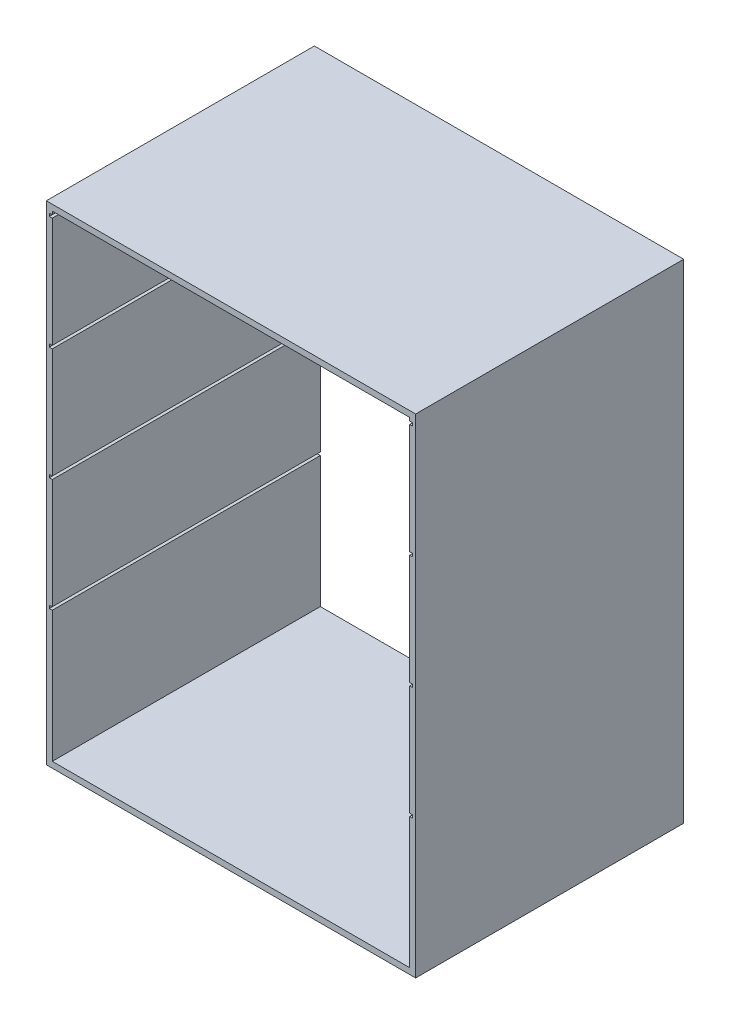
SolidWorks part; units mm, degrees
ref_plane "Front Plane" through (0, 0, 0) normal (0, 0, 1) x (1, 0, 0)
ref_plane "Top Plane" through (0, 0, 0) normal (0, 1, 0) x (1, 0, 0)
ref_plane "Right Plane" through (0, 0, 0) normal (1, 0, 0) x (0, 0, -1)
sketch "Sketch1" plane through (0, 0, 0) normal (0, 0, 1) x (1, 0, 0)
  line L1 (0, 0) -> (600, 0)
  line L2 (0, 0) -> (0, 800)
  line L3 (0, 800) -> (600, 800)
  line L4 (600, 0) -> (600, 800)
extrude "Extrude-Thin1" add sketch "Sketch1" along normal blind 450 thin
sketch "Sketch2" plane through (0, 0, 0) normal (0, 0, 1) x (1, 0, 0)
  line L0 (-5, 604.7007) -> (605, 604.7007)
  line L1 (-5, 604.7007) -> (-5, 599.7007)
  line L2 (-5, 599.7007) -> (605, 599.7007)
  line L3 (-5, 794.7007) -> (605, 794.7007)
  line L4 (605, 604.7007) -> (605, 599.7007)
  line L5 (-5, 414.7007) -> (605, 414.7007)
  line L6 (-5, 414.7007) -> (-5, 409.7007)
  line L7 (-5, 409.7007) -> (605, 409.7007)
  line L8 (605, 414.7007) -> (605, 409.7007)
  line L9 (-5, 224.7007) -> (605, 224.7007)
  line L10 (-5, 224.7007) -> (-5, 219.7007)
  line L11 (-5, 219.7007) -> (605, 219.7007)
  line L12 (605, 224.7007) -> (605, 219.7007)
  line L18 (-5, 794.7007) -> (-5, 789.7007)
  line L19 (-5, 789.7007) -> (605, 789.7007)
  line L20 (605, 794.7007) -> (605, 789.7007)
  dimension "D1" = 4
extrude "Cut-Extrude1" cut sketch "Sketch2" against normal blind 1000 and the other way blind 1000
ref_plane "Plane1" through (0, -10, 0) normal (0, -1, 0) x (-1, 0, 0)
sketch "Sketch3" plane through (0, -10, 0) normal (0, -1, 0) x (-1, 0, 0)
  circle A0 centre (-560, -50) radius 10
  circle A1 centre (-40, -50) radius 10
  circle A2 centre (-560, -400) radius 10
  circle A3 centre (-40, -400) radius 10
extrude "Cut-Extrude2" cut sketch "Sketch3" against normal blind 3
